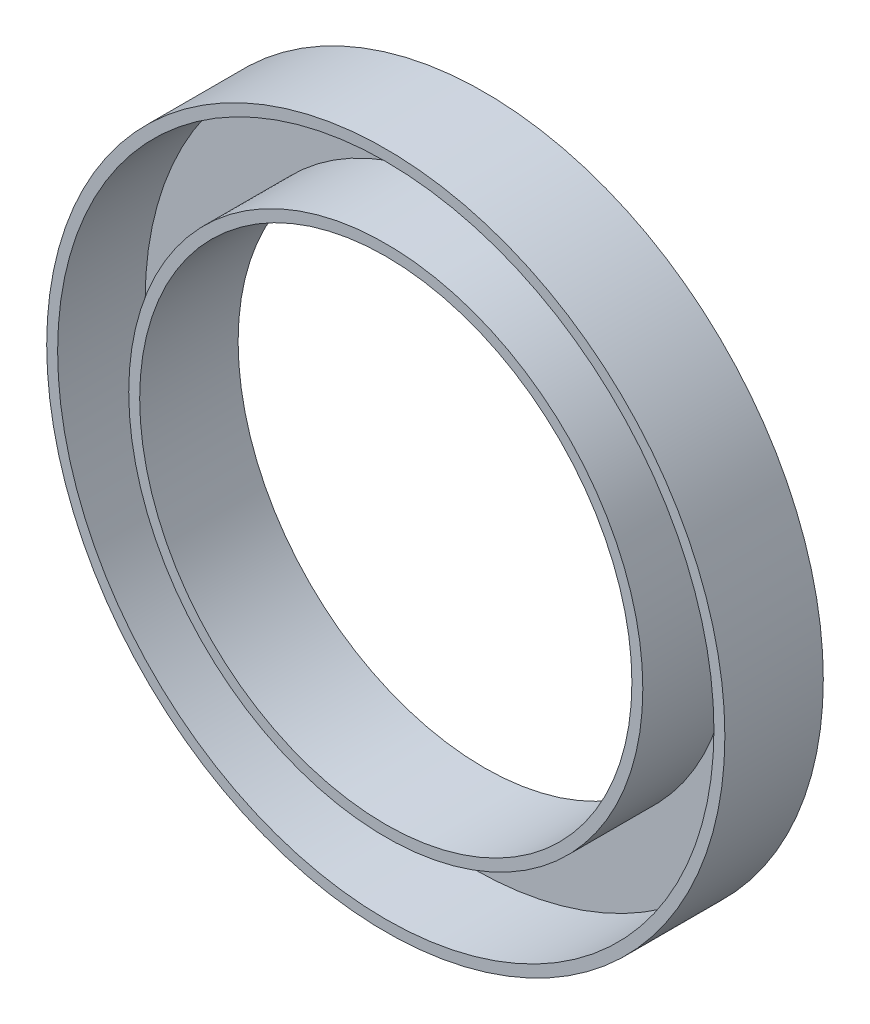
SolidWorks part; units mm, degrees
ref_plane "前视基准面" through (0, 0, 0) normal (0, 0, 1) x (1, 0, 0)
ref_plane "上视基准面" through (0, 0, 0) normal (0, 1, 0) x (1, 0, 0)
ref_plane "右视基准面" through (0, 0, 0) normal (1, 0, 0) x (0, 0, -1)
sketch "草图1" plane through (0, 0, 0) normal (0, 0, 1) x (1, 0, 0)
  circle A0 centre (0, 0) radius 22.5
  circle A1 centre (0, 0) radius 31
  dimension "D1" = 45
  dimension "D2" = 62
extrude "凸台-拉伸1" add sketch "草图1" along normal blind 9
shell "抽壳1" thickness 1
